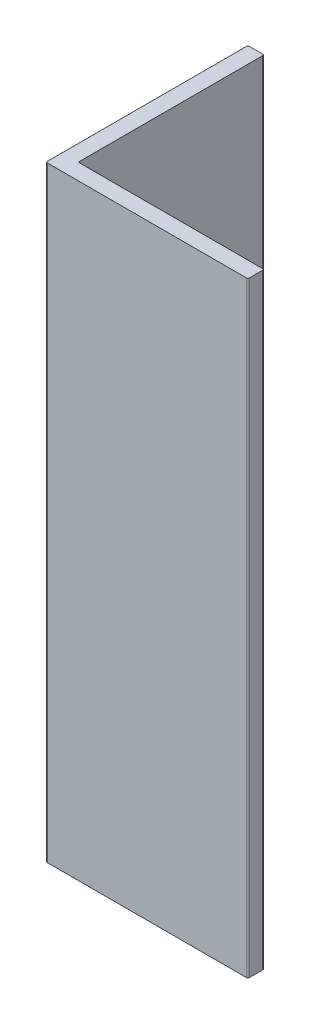
SolidWorks part; units mm, degrees
material "PVC Sztywny"
ref_plane "Płaszczyzna przednia" through (0, 0, 0) normal (0, 0, 1) x (1, 0, 0)
ref_plane "Płaszczyzna górna" through (0, 0, 0) normal (0, 1, 0) x (1, 0, 0)
ref_plane "Płaszczyzna prawa" through (0, 0, 0) normal (1, 0, 0) x (0, 0, -1)
sketch "Szkic1" plane through (0, 0, 0) normal (0, 1, 0) x (1, 0, 0)
  line L1 (0, 0) -> (15, 0)
  line L2 (0, 0) -> (0, 15)
  line L3 (0, 15) -> (1.2, 15)
  line L4 (15, 0) -> (15, 1.2)
  line L7 (15, 1.2) -> (1.2, 1.2)
  line L8 (1.2, 15) -> (1.2, 1.2)
  dimension "D1" = 15
  dimension "D2" = 1.2
  dimension "D3" = 1.2
extrude "Dodanie-wyciągnięcie1" add sketch "Szkic1" along normal blind 45
fillet "Zaokrąglenie2" radius 0.1 6 edges at (0, 22.5, -15) (1.2, 22.5, -1.2) (15, 22.5, -1.2) (15, 22.5, 0) (0, 22.5, 0) (1.2, 22.5, -15)
